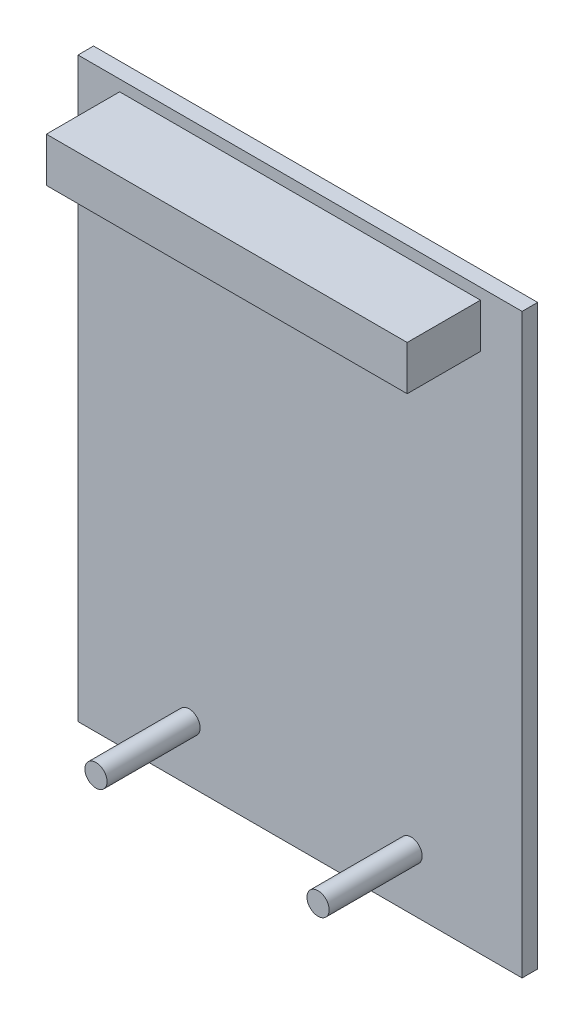
SolidWorks part; units mm, degrees
ref_plane "Front Plane" through (0, 0, 0) normal (0, 0, 1) x (1, 0, 0)
ref_plane "Top Plane" through (0, 0, 0) normal (0, 1, 0) x (1, 0, 0)
ref_plane "Right Plane" through (0, 0, 0) normal (1, 0, 0) x (0, 0, -1)
sketch "Sketch1" plane through (0, 0, 0) normal (0, 0, 1) x (1, 0, 0)
  line L1 (0, 66.04) -> (50.8, 66.04)
  line L2 (0, 66.04) -> (0, 0)
  line L3 (0, 0) -> (50.8, 0)
  line L4 (50.8, 66.04) -> (50.8, 0)
  dimension "D1" = 50.8
  dimension "D2" = 66.04
extrude "Boss-Extrude1" add sketch "Sketch1" along normal blind 1.778
sketch "Sketch2" plane through (0, 0, 1.778) normal (0, 0, 1) x (1, 0, 0)
  line L0 (25.4, 66.04) -> (25.4, 64.77) construction
  line L1 (4.7625, 64.77) -> (46.0375, 64.77)
  line L2 (4.7625, 64.77) -> (4.7625, 59.69)
  line L3 (4.7625, 59.69) -> (46.0375, 59.69)
  line L4 (46.0375, 64.77) -> (46.0375, 59.69)
  line L8 (50.8, 66.04) -> (0, 66.04) construction
  dimension "D1" = 5.08
  dimension "D2" = 41.275
  dimension "D3" = 1.27
extrude "Boss-Extrude2" add sketch "Sketch2" along normal blind 8.382
sketch "Sketch3" plane through (0, 0, 1.778) normal (0, 0, 1) x (1, 0, 0)
  line L0 (12.7, 6.35) -> (38.1, 6.35) construction
  line L1 (25.4, 6.35) -> (25.4, 0) construction
  line L3 (0, 0) -> (50.8, 0) construction
  circle A0 centre (12.7, 6.35) radius 1.27
  circle A1 centre (38.1, 6.35) radius 1.27
  dimension "D3" = 2.54
  dimension "D1" = 6.35
  dimension "D2" = 25.4
extrude "Boss-Extrude3" add sketch "Sketch3" along normal blind 10.6426
